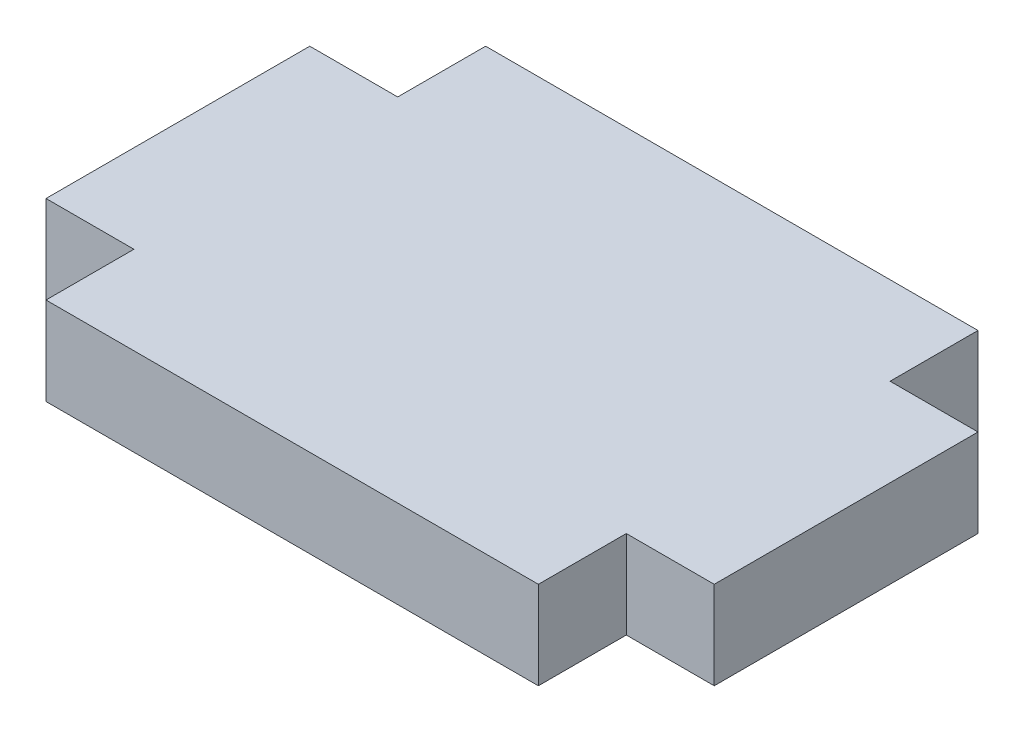
SolidWorks part; units mm, degrees
ref_plane "Front Plane" through (0, 0, 0) normal (0, 0, 1) x (1, 0, 0)
ref_plane "Top Plane" through (0, 0, 0) normal (0, 1, 0) x (1, 0, 0)
ref_plane "Right Plane" through (0, 0, 0) normal (1, 0, 0) x (0, 0, -1)
sketch "Sketch1" plane through (0, 0, 0) normal (0, 1, 0) x (1, 0, 0)
  line L0 (-8.89, 7.9375) -> (8.89, 7.9375)
  line L1 (8.89, 7.9375) -> (8.89, 4.7625)
  line L2 (8.89, 4.7625) -> (12.065, 4.7625)
  line L3 (12.065, 4.7625) -> (12.065, -4.7625)
  line L4 (12.065, -4.7625) -> (8.89, -4.7625)
  line L5 (8.89, -4.7625) -> (8.89, -7.9375)
  line L6 (8.89, -7.9375) -> (-8.89, -7.9375)
  line L7 (-8.89, -7.9375) -> (-8.89, -4.7625)
  line L8 (-8.89, -4.7625) -> (-12.065, -4.7625)
  line L9 (-12.065, -4.7625) -> (-12.065, 4.7625)
  line L10 (-12.065, 4.7625) -> (-8.89, 4.7625)
  line L11 (-8.89, 4.7625) -> (-8.89, 7.9375)
  point P12 (-12.065, 0)
  point P13 (0, -7.9375)
  dimension "D1" = 17.78
  dimension "D2" = 3.175
  dimension "D3" = 9.525
  dimension "D4" = 3.175
extrude "Boss-Extrude1" add sketch "Sketch1" along normal blind 3.175
